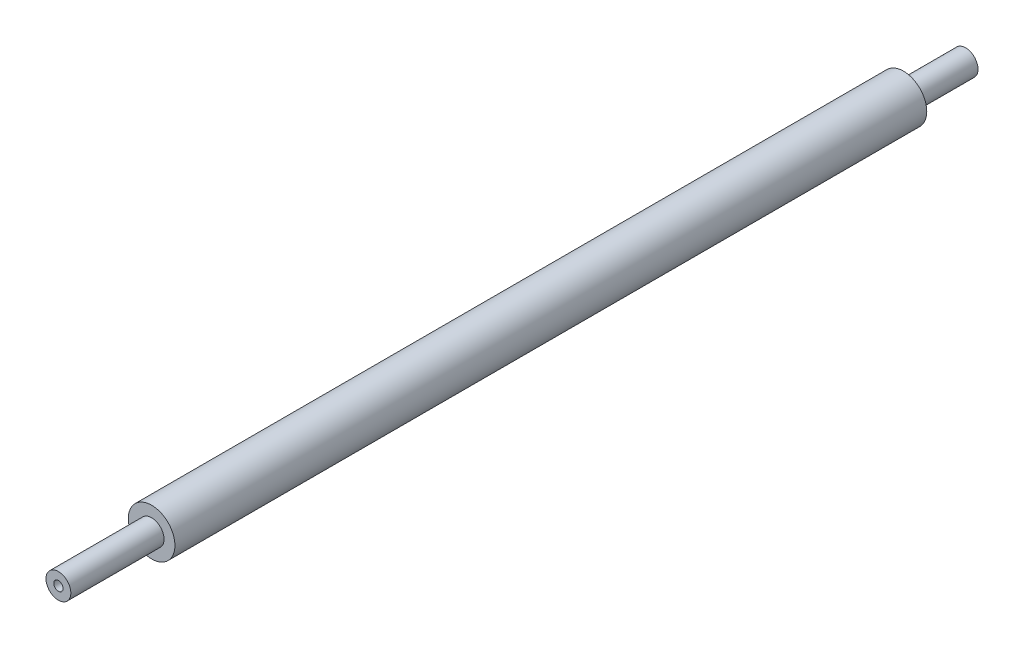
SolidWorks part; units mm, degrees
ref_plane "Front Plane" through (0, 0, 0) normal (0, 0, 1) x (1, 0, 0)
ref_plane "Top Plane" through (0, 0, 0) normal (0, 1, 0) x (1, 0, 0)
ref_plane "Right Plane" through (0, 0, 0) normal (1, 0, 0) x (0, 0, -1)
sketch "Sketch1" plane through (0, 0, 0) normal (0, 0, 1) x (1, 0, 0)
  circle A0 centre (0, 0) radius 7.5
  dimension "D1" = 15
extrude "Boss-Extrude1" add sketch "Sketch1" along normal blind 242
sketch "Sketch2" plane through (0, 0, 242) normal (0, 0, 1) x (1, 0, 0)
  circle A0 centre (0, 0) radius 4
  dimension "D1" = 8
extrude "Boss-Extrude2" add sketch "Sketch2" along normal blind 30
ref_plane "Plane1" through (0, 0, 121) normal (0, 0, 1) x (1, 0, 0)
sketch "Sketch3" plane through (0, 0, 0) normal (0, 0, -1) x (-1, 0, 0)
  circle A0 centre (0, 0) radius 4
  dimension "D1" = 8
extrude "Boss-Extrude3" add sketch "Sketch3" along normal blind 20 contours A0
sketch "Sketch4" plane through (0, 0, 272) normal (0, 0, 1) x (1, 0, 0)
  circle A0 centre (0, 0) radius 1.5
extrude "Cut-Extrude1" cut sketch "Sketch4" against normal blind 8
